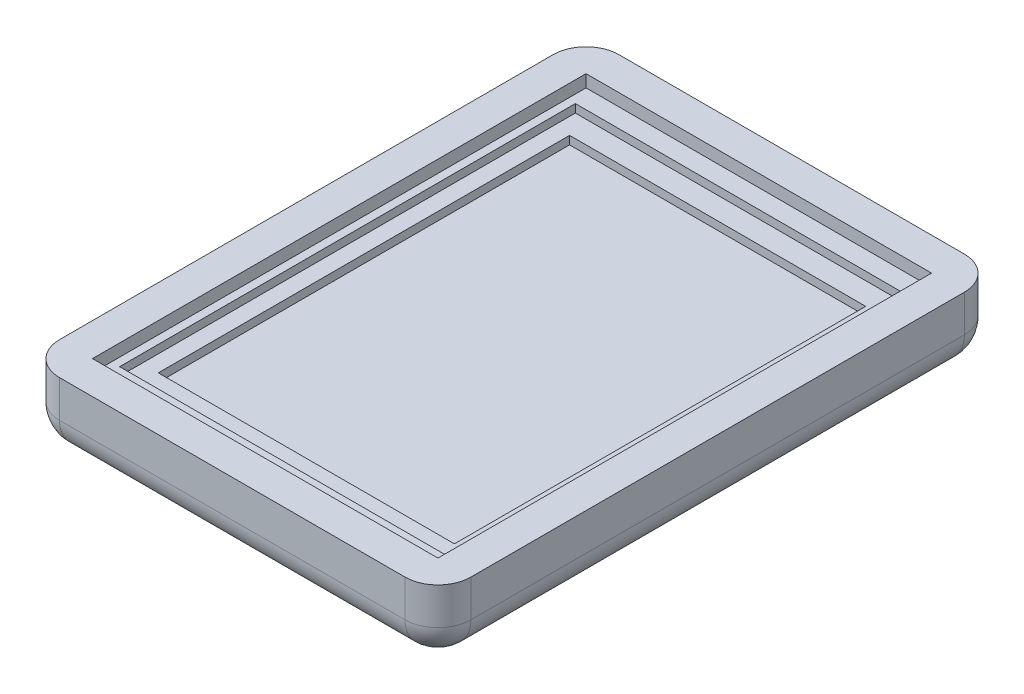
SolidWorks part; units mm, degrees
ref_plane "Front Plane" through (0, 0, 0) normal (0, 0, 1) x (1, 0, 0)
ref_plane "Top Plane" through (0, 0, 0) normal (0, 1, 0) x (1, 0, 0)
ref_plane "Right Plane" through (0, 0, 0) normal (1, 0, 0) x (0, 0, -1)
sketch "Sketch1" plane through (0, 0, 0) normal (0, 1, 0) x (1, 0, 0)
  line L1 (0, 0) -> (53.34, 0)
  line L2 (0, 0) -> (0, 76.2)
  line L3 (0, 76.2) -> (53.34, 76.2)
  line L4 (53.34, 0) -> (53.34, 76.2)
  line L5 (0, 0) -> (-5.08, 0)
  line L6 (0, 0) -> (0, -5.08)
  line L7 (0, -5.08) -> (-5.08, -5.08)
  line L8 (-5.08, 0) -> (-5.08, -5.08)
  line L9 (53.34, 76.2) -> (58.42, 76.2)
  line L10 (53.34, 76.2) -> (53.34, 81.28)
  line L11 (53.34, 81.28) -> (58.42, 81.28)
  line L12 (58.42, 76.2) -> (58.42, 81.28)
  line L13 (-5.08, -5.08) -> (58.42, -5.08)
  line L14 (-5.08, -5.08) -> (-5.08, 81.28)
  line L15 (-5.08, 81.28) -> (58.42, 81.28)
  line L16 (58.42, -5.08) -> (58.42, 81.28)
  dimension "D1" = 76.2
  dimension "D2" = 53.34
  dimension "D3" = 5.08
  dimension "D4" = 5.08
  dimension "D5" = 5.08
  dimension "D6" = 5.08
extrude "Boss-Extrude1" add sketch "Sketch1" against normal blind 5.715 contours L15 L14 L5 L2 L3 L10 | L13 L16 L9 L4 L1 L6 | L5 L8 L7 L6 | L9 L12 L11 L10
sketch "Sketch2" plane through (0, -5.715, 0) normal (0, -1, 0) x (-1, 0, 0)
  line L1 (5.08, 81.28) -> (-58.42, 81.28)
  line L2 (5.08, 81.28) -> (5.08, -5.08)
  line L3 (5.08, -5.08) -> (-58.42, -5.08)
  line L4 (-58.42, 81.28) -> (-58.42, -5.08)
extrude "Boss-Extrude2" add sketch "Sketch2" along normal blind 5.08
fillet "Fillet1" radius 5.08 8 edges at (-5.08, -5.3975, 5.08) (26.67, -10.795, 5.08) (58.42, -5.3975, 5.08) (58.42, -10.795, -38.1) (58.42, -5.3975, -81.28) (26.67, -10.795, -81.28) (-5.08, -5.3975, -81.28) (-5.08, -10.795, -38.1)
sketch "Sketch3" plane through (0, -5.715, 0) normal (0, 1, 0) x (1, 0, 0)
  line L1 (53.34, 76.2) -> (0, 76.2)
  line L2 (53.34, 76.2) -> (53.34, 0)
  line L3 (53.34, 0) -> (0, 0)
  line L4 (0, 76.2) -> (0, 0)
extrude "Boss-Extrude3" add sketch "Sketch3" along normal blind 3.81
sketch "Sketch4" plane through (0, -1.905, 0) normal (0, 1, 0) x (1, 0, 0)
  line L0 (53.34, 76.2) -> (0, 0)
  line L1 (0, 76.2) -> (53.34, 0)
  line L3 (1.27, 2.921) -> (52.07, 2.921)
  line L4 (1.27, 2.921) -> (1.27, 73.279)
  line L5 (1.27, 73.279) -> (52.07, 73.279)
  line L6 (52.07, 2.921) -> (52.07, 73.279)
  line L7 (1.27, 2.921) -> (52.07, 73.279) construction
  line L8 (1.27, 73.279) -> (52.07, 2.921) construction
  line L9 (3.81, 6.35) -> (49.53, 6.35)
  line L10 (3.81, 6.35) -> (3.81, 69.85)
  line L11 (3.81, 69.85) -> (49.53, 69.85)
  line L12 (49.53, 6.35) -> (49.53, 69.85)
  line L13 (3.81, 6.35) -> (49.53, 69.85) construction
  line L14 (3.81, 69.85) -> (49.53, 6.35) construction
  point P8 (26.67, 38.1)
  point P13 (26.67, 38.1)
extrude "Cut-Extrude1" cut sketch "Sketch4" against normal blind 1.27 contours L1 L11 L0 L5 | L12 L9 L1 L3 L6 L5 L0 L11 | L9 L0 L3 L1 | L10 L11 L1 L5 L4 L3 L0 L9
sketch "Sketch6" plane through (0, -1.905, 0) normal (0, 1, 0) x (1, 0, 0)
  line L1 (49.53, 69.85) -> (3.81, 69.85)
  line L2 (49.53, 69.85) -> (49.53, 6.35)
  line L3 (49.53, 6.35) -> (3.81, 6.35)
  line L4 (3.81, 69.85) -> (3.81, 6.35)
extrude "Cut-Extrude2" cut sketch "Sketch6" against normal blind 2.54
